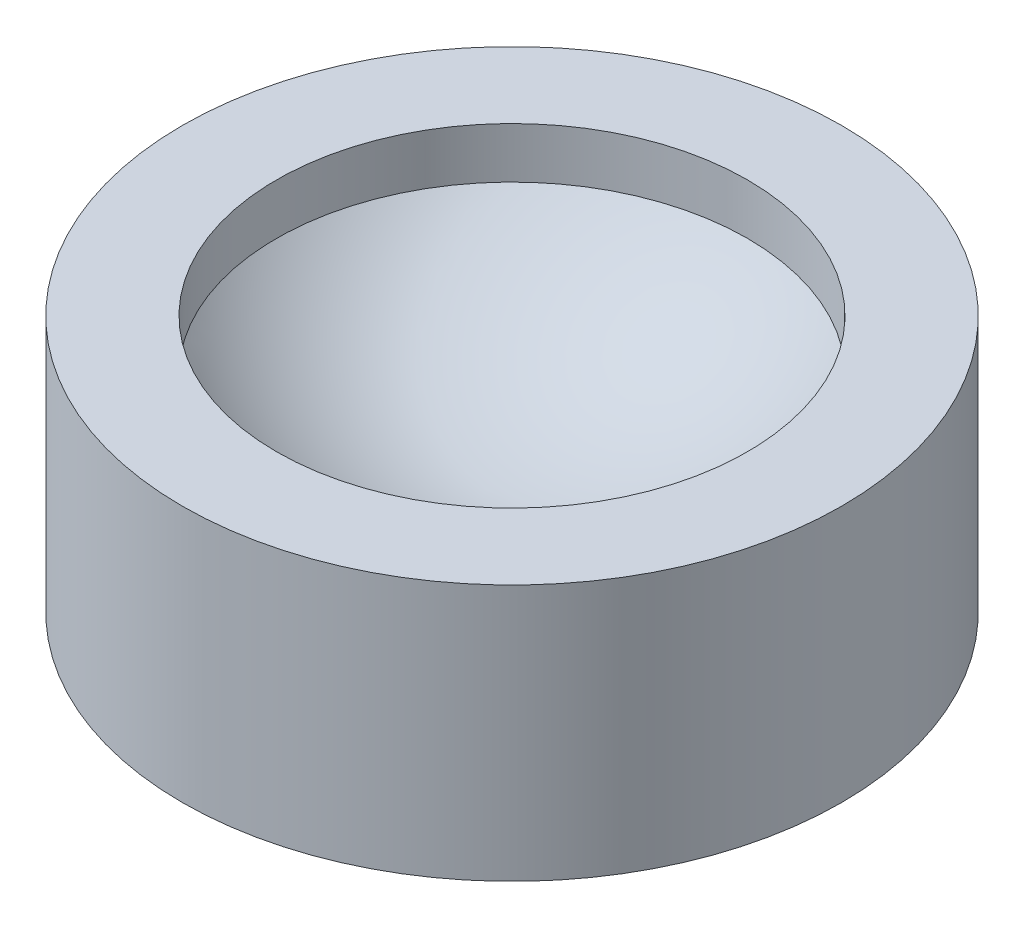
SolidWorks part; units mm, degrees
ref_plane "Front Plane" through (0, 0, 0) normal (0, 0, 1) x (1, 0, 0)
ref_plane "Top Plane" through (0, 0, 0) normal (0, 1, 0) x (1, 0, 0)
ref_plane "Right Plane" through (0, 0, 0) normal (1, 0, 0) x (0, 0, -1)
sketch "Sketch1" plane through (0, 0, 0) normal (0, 1, 0) x (1, 0, 0)
  circle A0 centre (0, 0) radius 10.5
  dimension "D1" = 21
extrude "Boss-Extrude1" add sketch "Sketch1" along normal blind 8.1741
sketch "Sketch2" plane through (0, 0, 0) normal (1, 0, 0) x (0, 0, -1)
  line L0 (0, 8.1741) -> (7.5, 8.1741)
  line L1 (7.5, 6.5597) -> (7.5, 8.1741)
  line L3 (0, 8.1741) -> (0, 3.1741)
  line L4 (-3.75, 3.1741) -> (-16.3292, 3.1741) construction
  arc A0 (0, 3.1741) -> (7.5, 6.5597) centre (0, 13.1741) ccw
  point P2 (0, 0)
  dimension "D4" = 10
  dimension "D1" = 7.5
  dimension "D2" = 8.1741
  dimension "D3" = 5
sketch "Sketch3" plane through (0, 0, 0) normal (0, 0, 1) x (1, 0, 0)
  line L0 (0, 0.0491) -> (0, 9.5041) construction
revolve "Cut-Revolve2" cut sketch "Sketch2" angle 360 about L0
equation "\"radius\"= 7.5 / 1000"
equation "\"D1@Sketch1\"=\"radius\"*2+.006"
equation "\"a\"= - 32.3127"
equation "\"b\"= .15"
equation "\"c\"=0.005"
equation "\"D1@Boss-Extrude1\" = \"depth\""
equation "\"D2@Sketch2\"=\"depth\""
equation "\"critical\"= - \"b\" / 2 / \"a\""
equation "\"critical_height\"= \"c\" + \"b\" * \"critical\" + \"a\" * \"critical\" ^ 2"
equation "\"center_height\"= \"c\""
equation "\"left_height\"= \"c\" + \"b\" * \"radius\" + \"a\" * \"radius\" ^ 2"
equation "\"max_height\"= \"critical_height\""
equation "\"min_height\"= \"center_height\""
equation "\"depth\"= 0.003 + \"c\" + \"max_height\" - \"min_height\""
equation "\"D3@Sketch2\"=5/1000"
